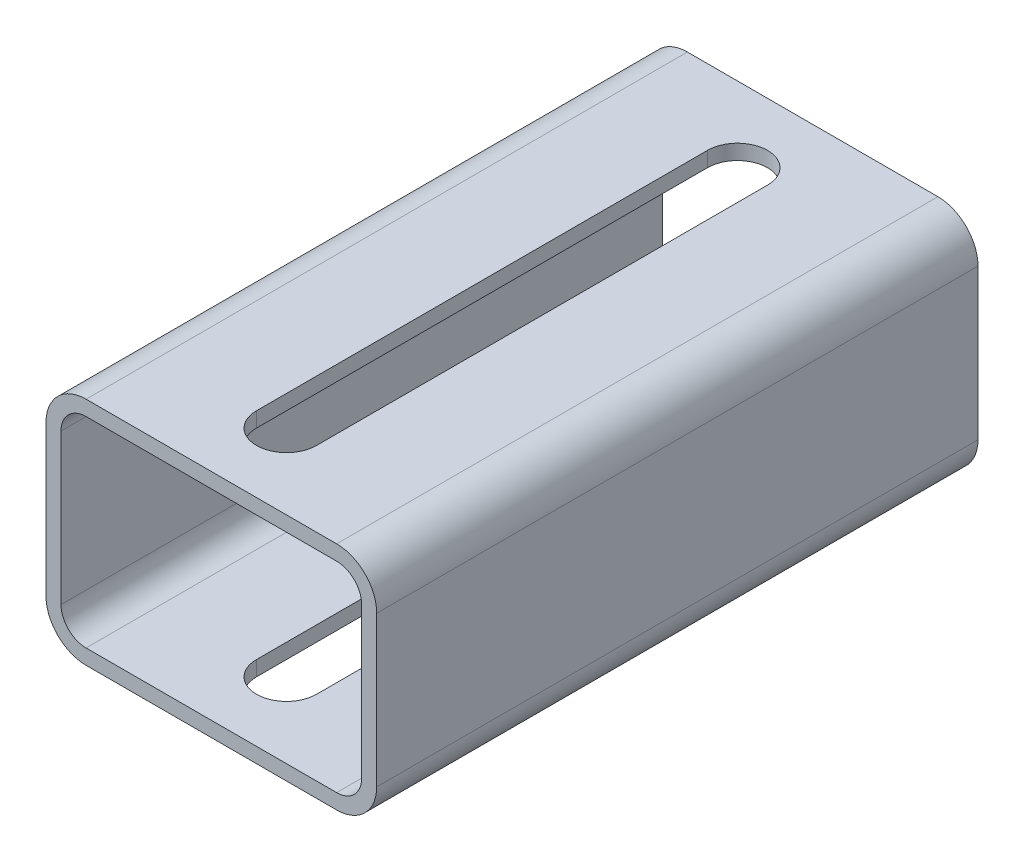
SolidWorks part; units mm, degrees
ref_plane "Front Plane" through (0, 0, 0) normal (0, 0, 1) x (1, 0, 0)
ref_plane "Top Plane" through (0, 0, 0) normal (0, 1, 0) x (1, 0, 0)
ref_plane "Right Plane" through (0, 0, 0) normal (1, 0, 0) x (0, 0, -1)
sketch "Sketch1" plane through (0, 0, 0) normal (0, 0, 1) x (1, 0, 0)
  line L1 (-25, -20) -> (25, -20)
  line L2 (-30, -15) -> (-30, 15)
  line L3 (-25, 20) -> (25, 20)
  line L4 (30, -15) -> (30, 15)
  line L5 (-30, -20) -> (30, 20) construction
  line L6 (-30, 20) -> (30, -20) construction
  arc A0 (-25, -20) -> (-30, -15) centre (-25, -15) cw
  arc A1 (25, -20) -> (30, -15) centre (25, -15) ccw
  arc A2 (25, 20) -> (30, 15) centre (25, 15) cw
  arc A3 (-30, 15) -> (-25, 20) centre (-25, 15) cw
  point P0 (0, 0)
  dimension "D1" = 5
  dimension "Width" = 50
  dimension "Length" = 40
extrude "Extrude-Thin1" add sketch "Sketch1" along normal mid plane 120 thin contours A3 L2 A0 L1 A1 L4 A2 L3
sketch "Sketch2" plane through (0, 23, 0) normal (0, 1, 0) x (1, 0, 0)
  line L0 (0, 45) -> (0, -45) construction
  line L1 (6, 45) -> (6, -45)
  line L2 (-6, 45) -> (-6, -45)
  arc A0 (6, 45) -> (-6, 45) centre (0, 45) ccw
  arc A1 (-6, -45) -> (6, -45) centre (0, -45) ccw
  point P3 (0, 0)
  dimension "D2" = 6
  dimension "D1" = 90
  dimension "D3" = 45
extrude "Cut-Extrude1" cut sketch "Sketch2" against normal through all and the other way through all
